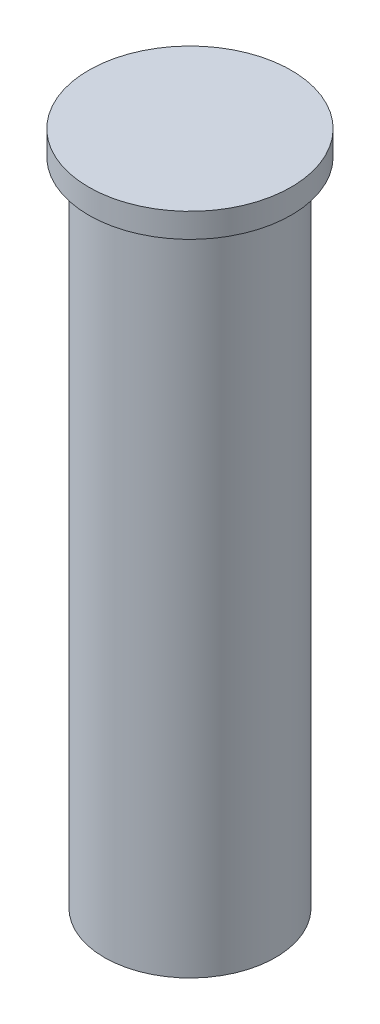
SolidWorks part; units mm, degrees
material "Plain Carbon Steel"
ref_plane "Front Plane" through (0, 0, 0) normal (0, 0, 1) x (1, 0, 0)
ref_plane "Top Plane" through (0, 0, 0) normal (0, 1, 0) x (1, 0, 0)
ref_plane "Right Plane" through (0, 0, 0) normal (1, 0, 0) x (0, 0, -1)
sketch "Sketch1" plane through (0, 0, 0) normal (0, 1, 0) x (1, 0, 0)
  circle A0 centre (0, 0) radius 4.7625
  dimension "D1" = 9.525
extrude "Boss-Extrude1" add sketch "Sketch1" along normal blind 1.143
sketch "Sketch2" plane through (0, 0, 0) normal (0, -1, 0) x (1, 0, 0)
  circle A0 centre (0, 0) radius 4.0259
  dimension "D1" = 8.0518
extrude "Boss-Extrude2" add sketch "Sketch2" along normal blind 31.75 from surface at -1.143 starting at face at (0, 1.143, 4.7625)
hole_wizard "#8-32 Tapped Hole1" positions "Sketch3" profile "Sketch5" tap size "#8-32" standard "ANSI Inch"
sketch "Sketch3" plane through (0, -30.607, 0) normal (0, -1, 0) x (-1, 0, 0)
  point P0 (0, 0)
sketch "Sketch5" plane through (0, -30.607, 0) normal (1, 0, 0) x (0, 0, -1)
  line L0 (0, 0) -> (0, 20.0878)
  line L1 (0, 20.0878) -> (1.7272, 19.05)
  line L2 (1.7272, 19.05) -> (1.7272, 2.3915)
  line L3 (1.7272, 2.3915) -> (2.7178, 0)
  line L5 (2.7178, 0) -> (0, 0)
  line L6 (-1.7272, 2.3915) -> (-2.7178, 0) construction
  line L10 (0, 20.0878) -> (-1.7272, 19.05) construction
  line L11 (0, -6.35) -> (0, 107.95) construction
  dimension "Tap Drill Dia." = 3.4544
  dimension "Tap Drill Depth" = 19.05
  dimension "Near C'Sink Dia." = 5.4356
  dimension "Near C'Sink Angle" = 45
  dimension "Drill Angle" = 118
cosmetic thread "Hole Thread1" parameters "D1"=16.002, "D2"=4.1656
